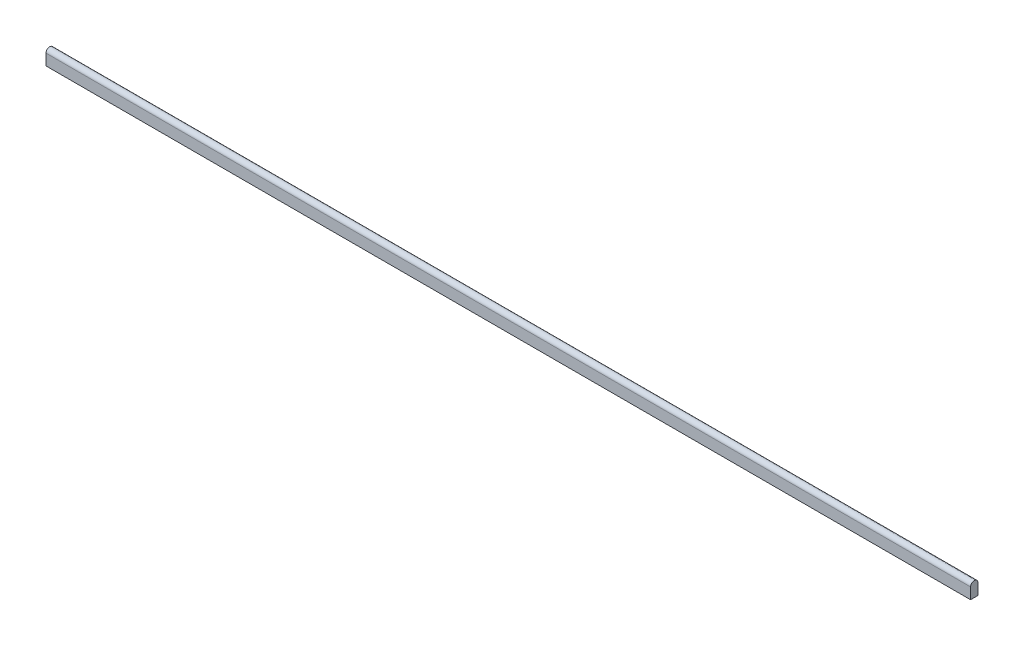
SolidWorks part; units mm, degrees
ref_plane "Plan de face" through (0, 0, 0) normal (0, 0, 1) x (1, 0, 0)
ref_plane "Plan de dessus" through (0, 0, 0) normal (0, 1, 0) x (1, 0, 0)
ref_plane "Plan de droite" through (0, 0, 0) normal (1, 0, 0) x (0, 0, -1)
sketch "Esquisse1" plane through (0, 0, 0) normal (1, 0, 0) x (0, 0, -1)
  line L0 (-2, 0) -> (-2, -6)
  line L1 (-2, -6) -> (2, -6)
  line L2 (2, -6) -> (2, 0)
  arc A0 (-2, 0) -> (2, 0) centre (0, 0) cw
  dimension "D1" = 2
  dimension "D2" = 6
extrude "Extrusion1" add sketch "Esquisse1" along normal blind 500
